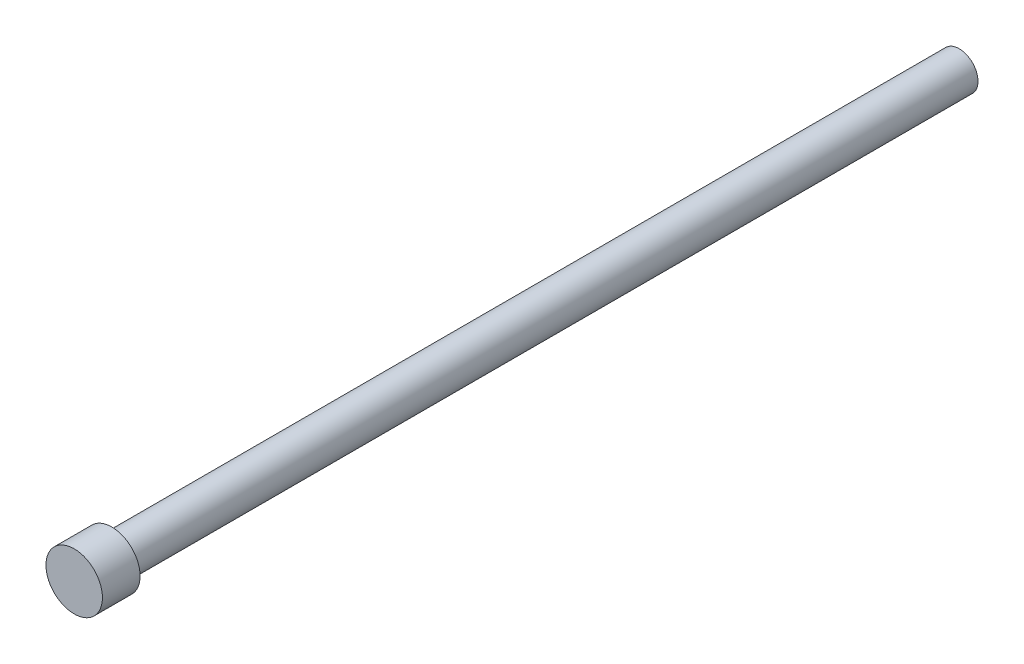
SolidWorks part; units mm, degrees
ref_plane "前基準面" through (0, 0, 0) normal (0, 0, 1) x (1, 0, 0)
ref_plane "上基準面" through (0, 0, 0) normal (0, 1, 0) x (1, 0, 0)
ref_plane "右基準面" through (0, 0, 0) normal (1, 0, 0) x (0, 0, -1)
sketch "草圖1" plane through (0, 0, 0) normal (0, 0, 1) x (1, 0, 0)
  circle A0 centre (0, 0) radius 1
  dimension "D1" = 2
extrude "填料-伸長1" add sketch "草圖1" along normal blind 45
ref_plane "平面1" through (0, 0, 45) normal (0, 0, 1) x (1, 0, 0)
sketch "草圖2" plane through (0, 0, 45) normal (0, 0, 1) x (1, 0, 0)
  circle A0 centre (0, 0) radius 1.5
  dimension "D1" = 3
extrude "填料-伸長2" add sketch "草圖2" along normal blind 2
ref_plane "平面2" through (0, 0, 0) normal (0, 0, -1) x (-1, 0, 0)
sketch "草圖3" plane through (0, 0, 0) normal (0, 0, -1) x (-1, 0, 0)
  circle A0 centre (0, 0) radius 0.75
  dimension "D1" = 1.5
extrude "除料-伸長1" cut sketch "草圖3" against normal blind 20
